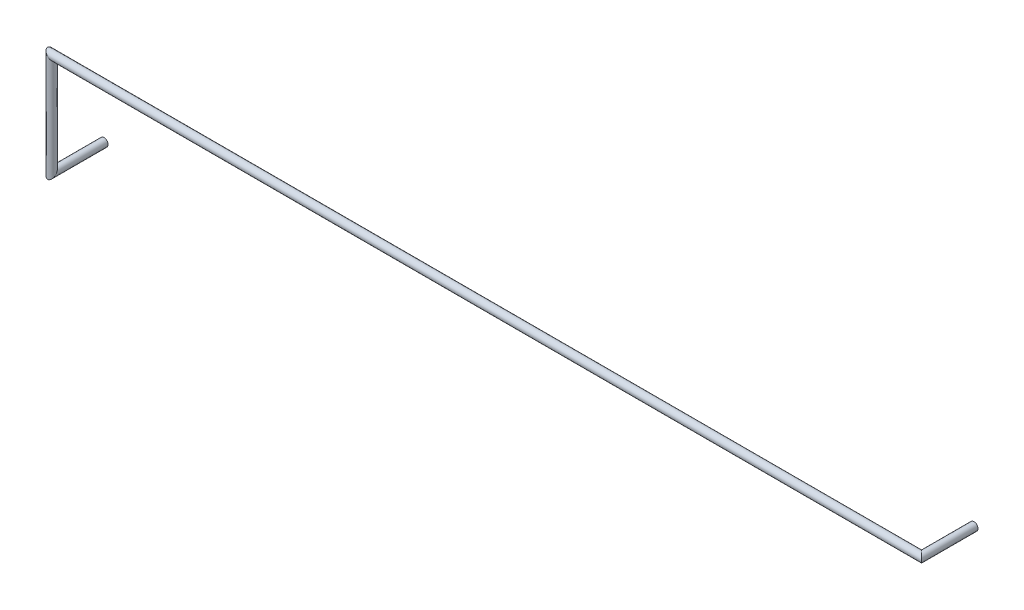
SolidWorks part; units mm, degrees
ref_plane "Front Plane" through (0, 0, 0) normal (0, 0, 1) x (1, 0, 0)
ref_plane "Top Plane" through (0, 0, 0) normal (0, 1, 0) x (1, 0, 0)
ref_plane "Right Plane" through (0, 0, 0) normal (1, 0, 0) x (0, 0, -1)
sketch3d "3DSketch3"
  line L0 (0, 0, 0) -> (0, 0, 2.6)
  line L1 (0, 0, 2.6) -> (0, 5.08, 2.6)
  line L2 (0, 5.08, 2.6) -> (43.18, 5.08, 2.6)
  line L3 (43.18, 5.08, 2.6) -> (43.18, 5.08, 0)
  dimension "D2" = 2.6
  dimension "D1" = 2.6
  dimension "D3" = 5.08
  dimension "D4" = 43.18
sweep "Sweep1" add path "3DSketch3" circular profile diameter 0.4 parameters "D3"=0.4
equation "\"D2@3DSketch3\"=\"D1@3DSketch3\""
equation "\"D3@3DSketch3\"=2.54*2"
equation "\"D4@3DSketch3\"=2.54*17"
